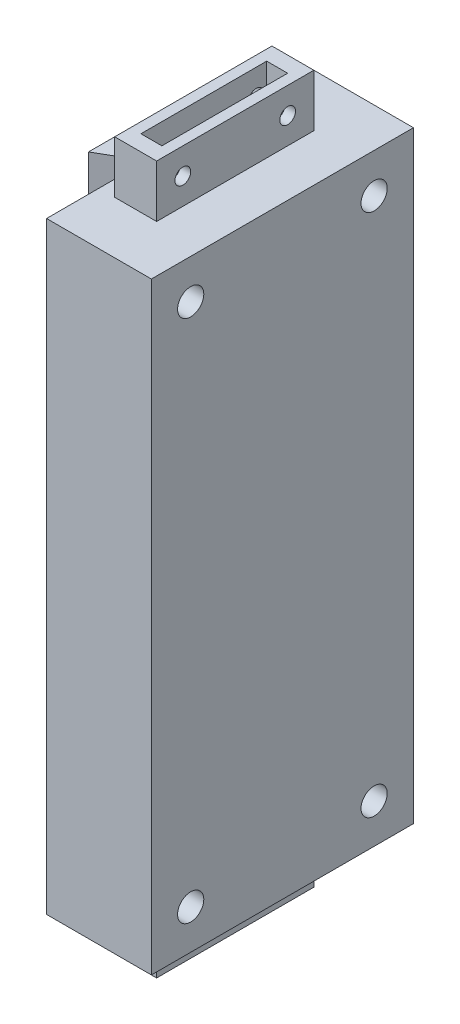
SolidWorks part; units mm, degrees
material "5052-H32"
ref_plane "Front Plane" through (0, 0, 0) normal (0, 0, 1) x (1, 0, 0)
ref_plane "Top Plane" through (0, 0, 0) normal (0, 1, 0) x (1, 0, 0)
ref_plane "Right Plane" through (0, 0, 0) normal (1, 0, 0) x (0, 0, -1)
sketch "Sketch1" plane through (0, 0, 0) normal (0, 1, 0) x (1, 0, 0)
  line L0 (-27, 10) -> (-27, -10)
  line L1 (-27, -10) -> (-20, -5.9585)
  line L2 (-20, -5.9585) -> (-20, -25)
  line L3 (-20, -25) -> (0, -25)
  line L4 (0, -25) -> (0, 25)
  line L5 (0, 25) -> (-20, 25)
  line L6 (-20, 25) -> (-20, 5.9585)
  line L7 (-20, 5.9585) -> (-27, 10)
  line L8 (-61.8655, 0) -> (80.92, 0) construction
  point P2 (0, 0)
  point P9 (-27, 0)
  dimension "D1" = 60
  dimension "D2" = 60
  dimension "D3" = 50
  dimension "D4" = 20
  dimension "D5" = 7
  dimension "D6" = 20
extrude "Boss-Extrude1" add sketch "Sketch1" along normal blind 115
sketch "Sketch2" plane through (0, 0, 0) normal (1, 0, 0) x (0, 0, -1)
  line L0 (-25, 115) -> (-25, 0) construction
  line L1 (-25, 115) -> (25, 115) construction
  line L2 (0, 103.7435) -> (0, -6.0358) construction
  line L3 (-40.2439, 50) -> (67.1156, 50) construction
  line L4 (-25, 0) -> (25, 0) construction
  circle A0 centre (-17.5, 107.5) radius 2.5
  circle A1 centre (-17.5, 7.5) radius 2.5
  circle A2 centre (17.5, 7.5) radius 2.5
  circle A3 centre (17.5, 107.5) radius 2.5
  dimension "D1" = 5
  dimension "D2" = 7.5
  dimension "D3" = 7.5
  dimension "D4" = 50
  dimension "D7" = 7.5
  dimension "D5" = 2
  dimension "D6" = 2
extrude "Cut-Extrude1" cut sketch "Sketch2" against normal blind 10
sketch "Sketch3" plane through (0, 115, 0) normal (0, 1, 0) x (1, 0, 0)
  line L0 (-17, 15) -> (-9, 15)
  line L1 (-9, 15) -> (-9, -15)
  line L2 (-9, -15) -> (-17, -15)
  line L3 (-17, -15) -> (-17, 15)
  line L4 (-20, -25) -> (0, -25) construction
  line L6 (0, -25) -> (0, 25) construction
  dimension "D1" = 8
  dimension "D2" = 30
  dimension "D3" = 10
  dimension "D4" = 9
extrude "Boss-Extrude2" add sketch "Sketch3" along normal blind 10
sketch "Sketch4" plane through (0, 0, 0) normal (0, -1, 0) x (1, 0, 0)
  line L0 (-17, 15) -> (-9, 15)
  line L1 (-9, 15) -> (-9, -15)
  line L2 (-9, -15) -> (-17, -15)
  line L3 (-17, -15) -> (-17, 15)
  line L4 (-20, 25) -> (0, 25) construction
  line L5 (0, -25) -> (-20, -25) construction
  line L6 (0, 25) -> (0, -25) construction
  dimension "D1" = 10
  dimension "D2" = 10
  dimension "D3" = 8
  dimension "D4" = 9
extrude "Boss-Extrude3" add sketch "Sketch4" along normal blind 10
sketch "Sketch5" plane through (0, -10, 0) normal (0, -1, 0) x (1, 0, 0)
  line L0 (-9, -15) -> (-9, 15) construction
  line L1 (-15, 12) -> (-11, 12)
  line L2 (-15, 12) -> (-15, -12)
  line L3 (-15, -12) -> (-11, -12)
  line L4 (-11, 12) -> (-11, -12)
  line L5 (-15, 12) -> (-11, -12) construction
  line L6 (-15, -12) -> (-11, 12) construction
  line L8 (-9, 15) -> (-17, 15) construction
  point P0 (-13, 0)
  dimension "D1" = 4
  dimension "D2" = 2
  dimension "D3" = 3
  dimension "D4" = 24
extrude "Cut-Extrude2" cut sketch "Sketch5" against normal blind 10
sketch "Sketch6" plane through (0, 125, 0) normal (0, 1, 0) x (1, 0, 0)
  line L0 (-9, 15) -> (-17, 15) construction
  line L1 (-15, 12) -> (-11, 12)
  line L2 (-15, 12) -> (-15, -12)
  line L3 (-15, -12) -> (-11, -12)
  line L4 (-11, 12) -> (-11, -12)
  line L5 (-15, 12) -> (-11, -12) construction
  line L6 (-15, -12) -> (-11, 12) construction
  line L7 (-17, -15) -> (-9, -15) construction
  line L8 (-9, -15) -> (-9, 15) construction
  point P0 (-13, 0)
  dimension "D1" = 4
  dimension "D2" = 3
  dimension "D3" = 3
  dimension "D4" = 2
extrude "Cut-Extrude3" cut sketch "Sketch6" against normal blind 10
sketch "Sketch7" plane through (0, 0, 0) normal (1, 0, 0) x (0, 0, -1)
  line L0 (0, 116.8171) -> (0, -14.4727) construction
  line L1 (-59.6864, 50) -> (76.9095, 50) construction
  line L2 (-25, 0) -> (25, 0) construction
  line L3 (15, -10) -> (-15, -10) construction
  line L4 (-15, 125) -> (15, 125) construction
  line L5 (-15, 125) -> (-15, 115) construction
  circle A0 centre (-10, 120) radius 1.5
  circle A1 centre (-10, -5) radius 1.5
  circle A2 centre (10, -5) radius 1.5
  circle A3 centre (10, 120) radius 1.5
  dimension "D1" = 3
  dimension "D2" = 50
  dimension "D3" = 5
  dimension "D4" = 5
  dimension "D7" = 20
  dimension "D8" = 5
  dimension "D5" = 2
  dimension "D6" = 2
extrude "Cut-Extrude4" cut sketch "Sketch7" against normal blind 32
